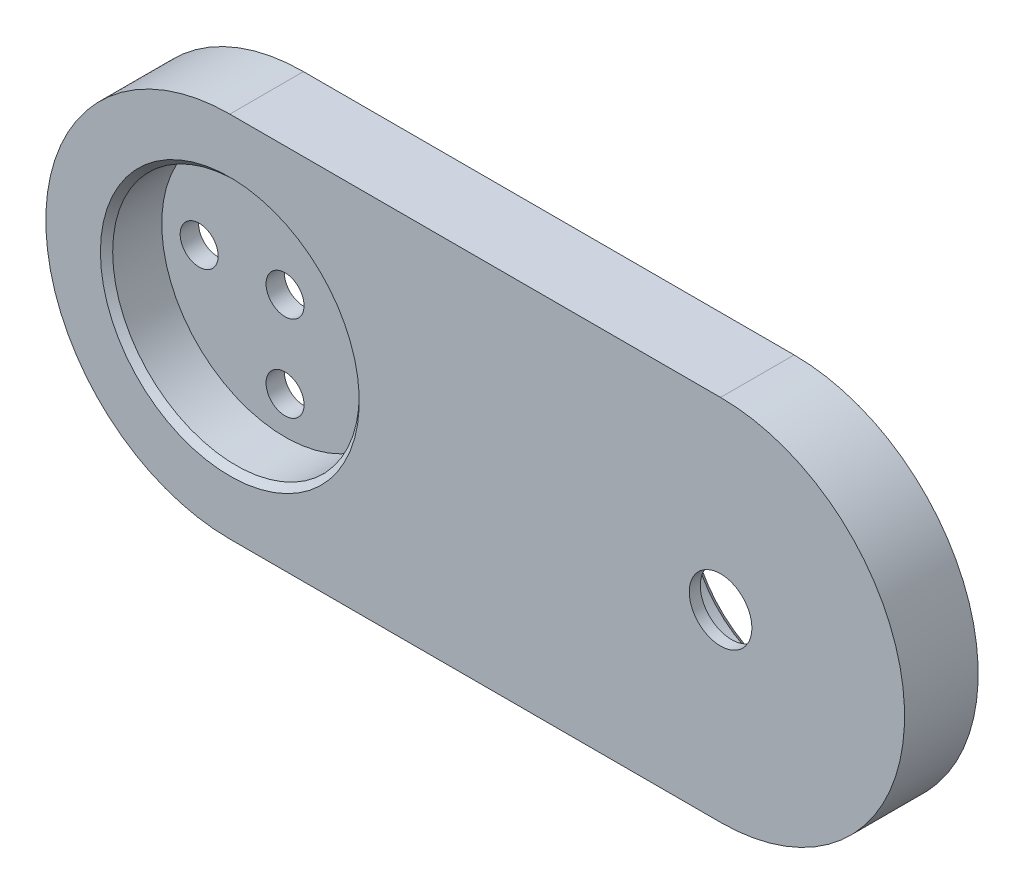
SolidWorks part; units mm, degrees
ref_plane "Front Plane" through (0, 0, 0) normal (0, 0, 1) x (1, 0, 0)
ref_plane "Top Plane" through (0, 0, 0) normal (0, 1, 0) x (1, 0, 0)
ref_plane "Right Plane" through (0, 0, 0) normal (1, 0, 0) x (0, 0, -1)
sketch "Sketch4" plane through (0, 0, 0) normal (0, 0, 1) x (1, 0, 0)
  line L0 (-20, 15) -> (20, 15)
  line L1 (20, -15) -> (-20, -15)
  line L2 (-20, 0) -> (20, 0) construction
  arc A0 (20, 15) -> (20, -15) centre (20, 0) cw
  arc A1 (-20, -15) -> (-20, 15) centre (-20, 0) cw
  dimension "D2" = 15
  dimension "D1" = 40
extrude "Boss-Extrude1" add sketch "Sketch4" along normal blind 6
sketch "Sketch8" plane through (0, 0, 6) normal (0, 0, 1) x (1, 0, 0)
  circle A0 centre (-20, 0) radius 10.05
  dimension "D1" = 20.1
extrude "Cut-Extrude4" cut sketch "Sketch8" against normal blind 4.5
sketch "Sketch9" plane through (0, 0, 0) normal (0, 0, -1) x (-1, 0, 0)
  circle A0 centre (-20, 0) radius 7.975
  dimension "D1" = 15.95
extrude "Cut-Extrude5" cut sketch "Sketch9" against normal blind 5.1
sketch "Sketch10" plane through (0, 0, 5.1) normal (0, 0, -1) x (-1, 0, 0)
  circle A0 centre (-20, 0) radius 2.55
  dimension "D1" = 5.1
extrude "Cut-Extrude6" cut sketch "Sketch10" against normal through all
sketch "Sketch11" plane through (0, 0, 1.5) normal (0, 0, 1) x (1, 0, 0)
  line L0 (-27, 0) -> (-13, 0) construction
  line L1 (-20, -7) -> (-20, 7) construction
  circle A0 centre (-20, 0) radius 1.55
  circle A1 centre (-13, 0) radius 1.55
  circle A2 centre (-27, 0) radius 1.55
  circle A3 centre (-20, 7) radius 1.55
  circle A4 centre (-20, -7) radius 1.55
  dimension "D1" = 3.1
  dimension "D2" = 14
extrude "Cut-Extrude7" cut sketch "Sketch11" against normal through all
chamfer "Chamfer1" distance 0.5 angle 45 2 edges at (12.025, 0, 0) (-9.95, 0, 6)
